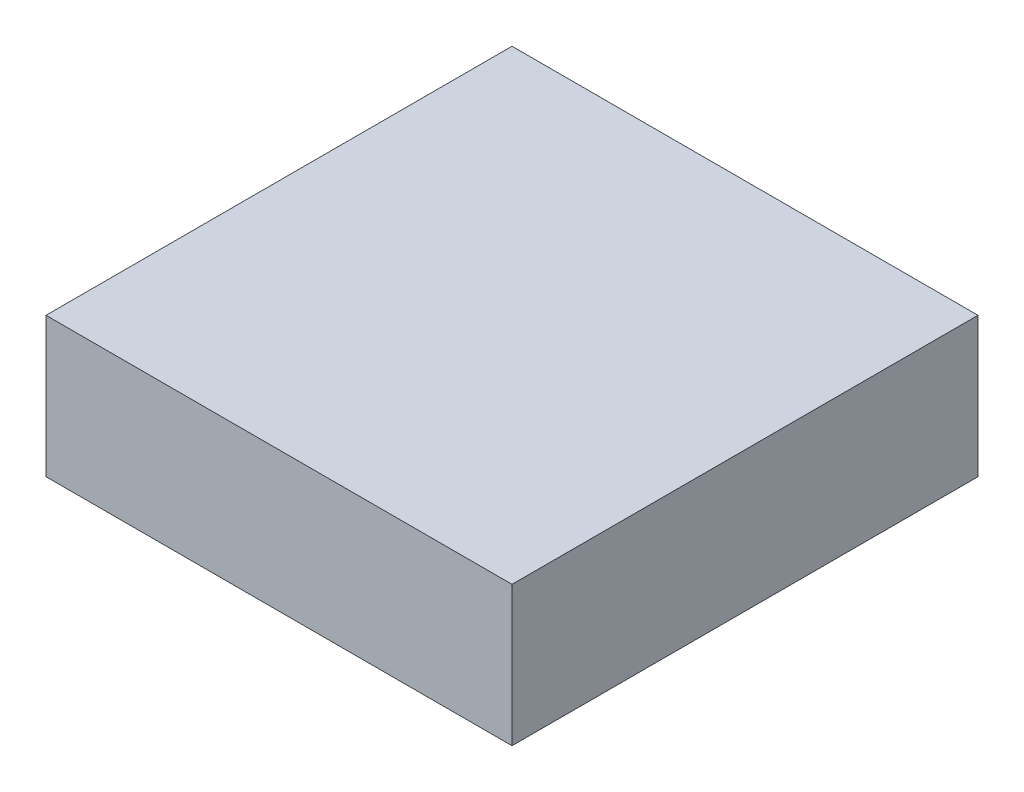
SolidWorks part; units mm, degrees
material "Plain Carbon Steel"
ref_plane "Front Plane" through (0, 0, 0) normal (0, 0, 1) x (1, 0, 0)
ref_plane "Top Plane" through (0, 0, 0) normal (0, 1, 0) x (1, 0, 0)
ref_plane "Right Plane" through (0, 0, 0) normal (1, 0, 0) x (0, 0, -1)
sketch "Sketch1" plane through (0, 0, 0) normal (0, 1, 0) x (1, 0, 0)
  line L1 (0, 0) -> (127, 0)
  line L2 (0, 0) -> (0, 127)
  line L3 (0, 127) -> (127, 127)
  line L4 (127, 0) -> (127, 127)
  dimension "D1" = 127
  dimension "D2" = 127
extrude "Boss-Extrude1" add sketch "Sketch1" along normal blind 38.1
